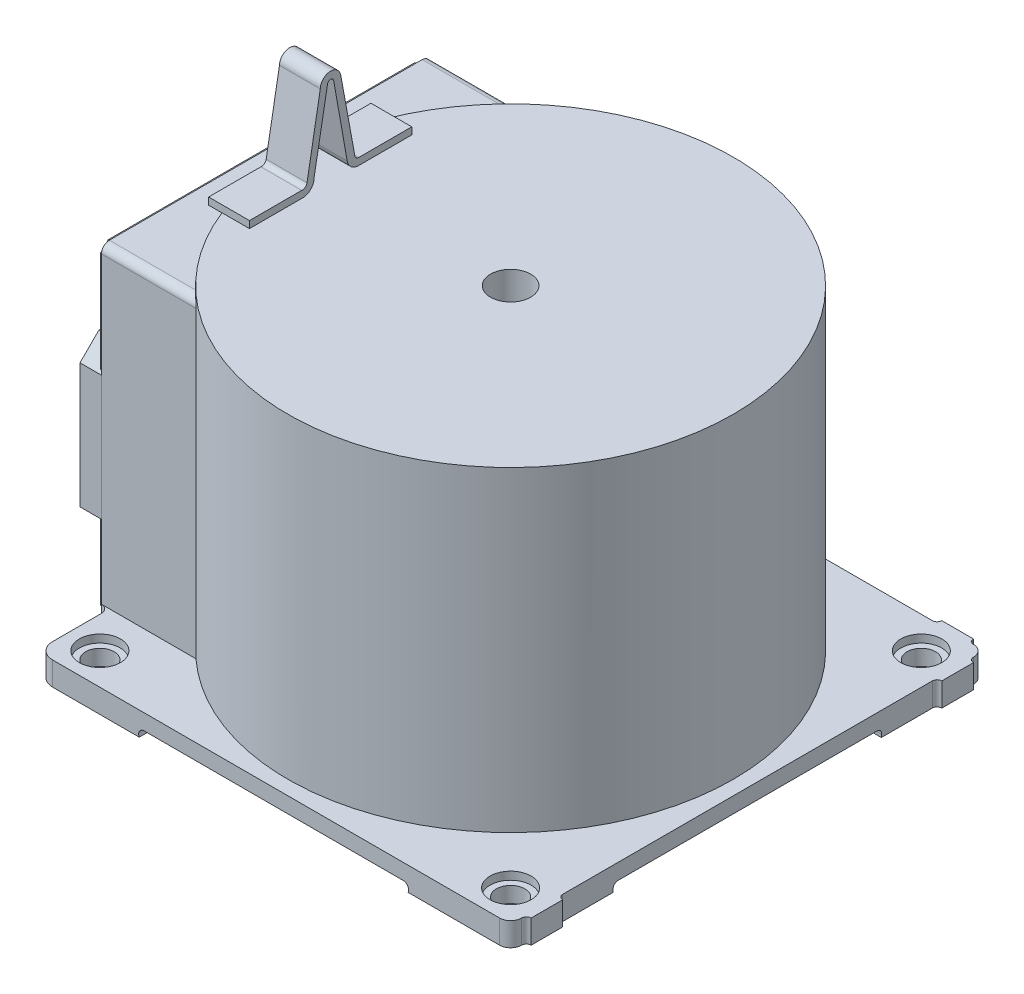
SolidWorks part; units mm, degrees
ref_plane "FRONT" through (0, 0, 0) normal (0, 0, 1) x (1, 0, 0)
ref_plane "TOP" through (0, 0, 0) normal (0, 1, 0) x (1, 0, 0)
ref_plane "SIDE" through (0, 0, 0) normal (1, 0, 0) x (0, 0, -1)
sketch "Sketch1"
sketch "Sketch2"
sketch "Sketch5"
sketch "Sketch3" plane through (0, 0, 0) normal (0, 1, 0) x (1, 0, 0)
  line L0 (140, 153) -> (120, 153)
  line L1 (-117, 150) -> (117, 150)
  line L2 (117, 150) -> (-117, 150) construction
  line L3 (153, 140) -> (153, 120)
  line L4 (150, 117) -> (150, -117)
  line L5 (150, 117) -> (150, -117) construction
  line L6 (153, -120) -> (153, -140)
  line L7 (143, -150) -> (-140, -150)
  line L8 (-140, -150) -> (143, -150) construction
  line L9 (-150, -140) -> (-150, -109)
  line L10 (-155, -104) -> (-155, 104)
  line L11 (-155, 104) -> (-155, -104) construction
  line L12 (-120, 153) -> (-140, 153)
  line L13 (-150, 143) -> (-150, 109)
  arc A0 (117, 150) -> (120, 153) centre (117, 153) ccw
  arc A1 (153, 140) -> (150, 143) centre (153, 143) cw
  arc A2 (150, 143) -> (143, 150) centre (143, 143) ccw
  arc A3 (143, 150) -> (140, 153) centre (143, 153) cw
  arc A4 (150, 117) -> (153, 120) centre (153, 117) cw
  arc A5 (150, -117) -> (153, -120) centre (153, -117) ccw
  arc A6 (153, -140) -> (150, -143) centre (153, -143) ccw
  arc A7 (150, -143) -> (143, -150) centre (143, -143) cw
  arc A8 (-140, -150) -> (-150, -140) centre (-140, -140) cw
  arc A9 (-150, -109) -> (-155, -104) centre (-155, -109) ccw
  arc A10 (-150, 109) -> (-155, 104) centre (-155, 109) cw
  arc A11 (-150, 143) -> (-143, 150) centre (-143, 143) cw
  arc A12 (-143, 150) -> (-140, 153) centre (-143, 153) ccw
  arc A13 (-117, 150) -> (-120, 153) centre (-117, 153) cw
extrude "Base-Extrude" add sketch "Sketch3" along normal blind 14.9225
sketch "Sketch4" plane through (0, 0, 150) normal (0, 0, 1) x (1, 0, 0)
  line L0 (82, 5) -> (-82, 5)
  line L1 (85.09, 0) -> (85.09, -16.51)
  line L2 (85.09, -16.51) -> (-85.09, -16.51)
  line L3 (-85.09, -16.51) -> (-85.09, 0)
  arc A0 (-82, 5) -> (-85.09, 0) centre (-82, 1.5452) ccw
  arc A1 (82, 5) -> (85.09, 0) centre (82, 1.5452) cw
extrude "Cut-Extrude1" cut sketch "Sketch4" against normal through all
sketch "Sketch6" plane through (150, 0, 0) normal (1, 0, 0) x (0, 0, -1)
  line L0 (82.0005, 5.0001) -> (-82.0005, 5.0001)
  line L1 (84.6883, 1.8556) -> (84.6883, -4.2544)
  line L2 (84.6883, -4.2544) -> (-85.09, -4.2544)
  line L3 (-85.09, -4.2544) -> (-85.09, 1.27)
  arc A0 (-82.0005, 5.0001) -> (-85.09, 1.27) centre (-82.0005, 1.8556) ccw
  arc A1 (82.0005, 5.0001) -> (84.6883, 1.8556) centre (82.0005, 2.2792) cw
extrude "Cut-Extrude2" cut sketch "Sketch6" against normal through all
sketch "Sketch7" plane through (0, 14.9225, 0) normal (0, 1, 0) x (-1, 0, 0)
  circle A0 centre (-130, 130) radius 13
  circle A1 centre (-130, -130) radius 13
  circle A2 centre (130, -130) radius 13
  circle A3 centre (130, 130) radius 13
  circle A4 centre (-130, -130) radius 13 construction
  circle A5 centre (-130, 130) radius 13 construction
  circle A6 centre (130, 130) radius 13 construction
  circle A7 centre (130, -130) radius 13 construction
extrude "Cut-Extrude3" cut sketch "Sketch7" against normal blind 5
sketch "Sketch8" plane through (0, 9.9225, 0) normal (0, 1, 0) x (-1, 0, 0)
  circle A0 centre (-130, -130) radius 9
  circle A1 centre (130, -130) radius 9
  circle A2 centre (130, 130) radius 9
  circle A3 centre (-130, 130) radius 9
  circle A4 centre (130, -130) radius 9 construction
  circle A5 centre (-130, -130) radius 9 construction
  circle A6 centre (-130, 130) radius 9 construction
  circle A7 centre (130, 130) radius 9 construction
extrude "Cut-Extrude4" cut sketch "Sketch8" against normal through all
sketch "Sketch9" plane through (0, 14.9225, 0) normal (0, 1, 0) x (-1, 0, 0)
  circle A0 centre (0, 0) radius 141
  circle A1 centre (0, 0) radius 141 construction
extrude "Boss-Extrude1" add sketch "Sketch9" along normal blind 200.152
sketch "Sketch10" plane through (-155, 0, 0) normal (-1, 0, 0) x (0, 0, 1)
  line L0 (99, 212) -> (-99, 212)
  line L1 (-104, 207) -> (-104, 10)
  line L2 (-99, 5) -> (99, 5)
  line L3 (104, 10) -> (104, 207)
  arc A0 (104, 207) -> (99, 212) centre (99, 207) ccw
  arc A1 (-99, 212) -> (-104, 207) centre (-99, 207) ccw
  arc A2 (-104, 10) -> (-99, 5) centre (-99, 10) ccw
  arc A3 (99, 5) -> (104, 10) centre (99, 10) ccw
extrude "Boss-Extrude2" add sketch "Sketch10" against normal up to surface (59.7897 mm away)
sketch "Sketch11" plane through (-155, 0, 0) normal (-1, 0, 0) x (0, 0, 1)
  line L0 (91.5, 152) -> (12.5, 152)
  line L1 (91.5, 152) -> (103.5, 140)
  line L2 (103.5, 140) -> (103.5, 61)
  line L3 (103.5, 61) -> (91.5, 49)
  line L4 (91.5, 49) -> (12.5, 49)
  line L5 (52, 152) -> (52, 112.256) construction
  line L6 (0.5, 140) -> (0.5, 61)
  line L7 (0.5, 140) -> (12.5, 152)
  line L8 (12.5, 49) -> (0.5, 61)
extrude "Boss-Extrude3" add sketch "Sketch11" along normal blind 14.097
sketch "Sketch12" plane through (-155, 0, 0) normal (-1, 0, 0) x (0, 0, 1)
  line L0 (-97, 210) -> (97, 210)
  line L1 (97, 210) -> (102, 205)
  line L2 (102, 205) -> (102, 12)
  line L3 (102, 12) -> (97, 7)
  line L4 (97, 7) -> (-77, 7)
  line L5 (-77, 7) -> (-82, 12)
  line L6 (-82, 12) -> (-82, 26)
  line L7 (-82, 26) -> (-97, 26)
  line L8 (-97, 26) -> (-102, 31)
  line L9 (-102, 31) -> (-102, 205)
  line L10 (-102, 205) -> (-97, 210)
extrude "Boss-Extrude4" add sketch "Sketch12" along normal blind 2.667
sketch "Sketch13" plane through (-157.667, 0, 0) normal (-1, 0, 0) x (0, 0, 1)
  line L0 (-11.5, 119) -> (-11.5, 152)
  line L1 (-16.5, 157) -> (-79.5, 157)
  line L2 (-84.5, 152) -> (-84.5, 119)
  line L4 (-79.5, 114) -> (-16.5, 114)
  line L5 (-79.5, 87.5) -> (-16.5, 87.5)
  line L6 (-11.5, 82.5) -> (-11.5, 49.5)
  line L8 (-16.5, 44.5) -> (-79.5, 44.5)
  line L9 (-84.5, 49.5) -> (-84.5, 82.5)
  arc A0 (-16.5, 157) -> (-11.5, 152) centre (-16.5, 152) cw
  arc A1 (-11.5, 119) -> (-16.5, 114) centre (-16.5, 119) cw
  arc A2 (-79.5, 114) -> (-84.5, 119) centre (-79.5, 119) cw
  arc A3 (-84.5, 152) -> (-79.5, 157) centre (-79.5, 152) cw
  arc A4 (-84.5, 82.5) -> (-79.5, 87.5) centre (-79.5, 82.5) cw
  arc A5 (-16.5, 87.5) -> (-11.5, 82.5) centre (-16.5, 82.5) cw
  arc A6 (-11.5, 49.5) -> (-16.5, 44.5) centre (-16.5, 49.5) cw
  arc A7 (-79.5, 44.5) -> (-84.5, 49.5) centre (-79.5, 49.5) cw
extrude "Boss-Extrude5" add sketch "Sketch13" along normal blind 34.0995
sketch "Sketch14" plane through (-191.7665, 0, 0) normal (-1, 0, 0) x (0, 0, 1)
  line L0 (-80.5, 152) -> (-80.5, 119) construction
  line L1 (-80.5, 153) -> (-15.5, 153)
  line L2 (-80.5, 153) -> (-80.5, 118)
  line L3 (-80.5, 118) -> (-15.5, 118)
  line L4 (-15.5, 153) -> (-15.5, 118)
  line L5 (-80.5, 48.5) -> (-15.5, 48.5)
  line L6 (-80.5, 48.5) -> (-80.5, 83.5)
  line L7 (-80.5, 83.5) -> (-15.5, 83.5)
  line L8 (-15.5, 48.5) -> (-15.5, 83.5)
  line L9 (-15.5, 119) -> (-15.5, 152) construction
  line L10 (-79.5, 153) -> (-48, 153) construction
  line L11 (-79.5, 118) -> (-48, 118) construction
  line L12 (-79.5, 83.5) -> (-48, 83.5) construction
  line L13 (-79.5, 48.5) -> (-48, 48.5) construction
  line L14 (-61.5, 124.25) -> (-57.0042, 124.25) construction
  line L15 (-61.5, 124.25) -> (-61.5, 128.7458) construction
  line L16 (-61.5, 54.75) -> (-57.0042, 54.75) construction
  line L17 (-61.5, 54.75) -> (-61.5, 59.2458) construction
  circle A0 centre (-61.5, 124.25) radius 1.75
  circle A1 centre (-61.5, 124.25) radius 1.75 construction
  circle A2 centre (-57.0042, 124.25) radius 1.75
  circle A3 centre (-52.5084, 124.25) radius 1.75
  circle A4 centre (-48.0126, 124.25) radius 1.75
  circle A5 centre (-43.5168, 124.25) radius 1.75
  circle A6 centre (-39.021, 124.25) radius 1.75
  circle A7 centre (-34.5252, 124.25) radius 1.75
  circle A8 centre (-61.5, 128.7458) radius 1.75
  circle A9 centre (-57.0042, 128.7458) radius 1.75
  circle A10 centre (-52.5084, 128.7458) radius 1.75
  circle A11 centre (-48.0126, 128.7458) radius 1.75
  circle A12 centre (-43.5168, 128.7458) radius 1.75
  circle A13 centre (-39.021, 128.7458) radius 1.75
  circle A14 centre (-34.5252, 128.7458) radius 1.75
  circle A15 centre (-61.5, 133.2416) radius 1.75
  circle A16 centre (-57.0042, 133.2416) radius 1.75
  circle A17 centre (-52.5084, 133.2416) radius 1.75
  circle A18 centre (-48.0126, 133.2416) radius 1.75
  circle A19 centre (-43.5168, 133.2416) radius 1.75
  circle A20 centre (-39.021, 133.2416) radius 1.75
  circle A21 centre (-34.5252, 133.2416) radius 1.75
  circle A22 centre (-61.5, 137.7374) radius 1.75
  circle A23 centre (-57.0042, 137.7374) radius 1.75
  circle A24 centre (-52.5084, 137.7374) radius 1.75
  circle A25 centre (-48.0126, 137.7374) radius 1.75
  circle A26 centre (-43.5168, 137.7374) radius 1.75
  circle A27 centre (-39.021, 137.7374) radius 1.75
  circle A28 centre (-34.5252, 137.7374) radius 1.75
  circle A29 centre (-61.5, 142.2332) radius 1.75
  circle A30 centre (-57.0042, 142.2332) radius 1.75
  circle A31 centre (-52.5084, 142.2332) radius 1.75
  circle A32 centre (-48.0126, 142.2332) radius 1.75
  circle A33 centre (-43.5168, 142.2332) radius 1.75
  circle A34 centre (-39.021, 142.2332) radius 1.75
  circle A35 centre (-34.5252, 142.2332) radius 1.75
  circle A36 centre (-61.5, 146.729) radius 1.75
  circle A37 centre (-57.0042, 146.729) radius 1.75
  circle A38 centre (-52.5084, 146.729) radius 1.75
  circle A39 centre (-48.0126, 146.729) radius 1.75
  circle A40 centre (-43.5168, 146.729) radius 1.75
  circle A41 centre (-39.021, 146.729) radius 1.75
  circle A42 centre (-34.5252, 146.729) radius 1.75
  circle A43 centre (-61.5, 54.75) radius 1.75
  circle A44 centre (-61.5, 54.75) radius 1.75 construction
  circle A45 centre (-57.0042, 54.75) radius 1.75
  circle A46 centre (-52.5084, 54.75) radius 1.75
  circle A47 centre (-48.0126, 54.75) radius 1.75
  circle A48 centre (-43.5168, 54.75) radius 1.75
  circle A49 centre (-39.021, 54.75) radius 1.75
  circle A50 centre (-34.5252, 54.75) radius 1.75
  circle A51 centre (-61.5, 59.2458) radius 1.75
  circle A52 centre (-57.0042, 59.2458) radius 1.75
  circle A53 centre (-52.5084, 59.2458) radius 1.75
  circle A54 centre (-48.0126, 59.2458) radius 1.75
  circle A55 centre (-43.5168, 59.2458) radius 1.75
  circle A56 centre (-39.021, 59.2458) radius 1.75
  circle A57 centre (-34.5252, 59.2458) radius 1.75
  circle A58 centre (-61.5, 63.7416) radius 1.75
  circle A59 centre (-57.0042, 63.7416) radius 1.75
  circle A60 centre (-52.5084, 63.7416) radius 1.75
  circle A61 centre (-48.0126, 63.7416) radius 1.75
  circle A62 centre (-43.5168, 63.7416) radius 1.75
  circle A63 centre (-39.021, 63.7416) radius 1.75
  circle A64 centre (-34.5252, 63.7416) radius 1.75
  circle A65 centre (-61.5, 68.2374) radius 1.75
  circle A66 centre (-57.0042, 68.2374) radius 1.75
  circle A67 centre (-52.5084, 68.2374) radius 1.75
  circle A68 centre (-48.0126, 68.2374) radius 1.75
  circle A69 centre (-43.5168, 68.2374) radius 1.75
  circle A70 centre (-39.021, 68.2374) radius 1.75
  circle A71 centre (-34.5252, 68.2374) radius 1.75
  circle A72 centre (-61.5, 72.7332) radius 1.75
  circle A73 centre (-57.0042, 72.7332) radius 1.75
  circle A74 centre (-52.5084, 72.7332) radius 1.75
  circle A75 centre (-48.0126, 72.7332) radius 1.75
  circle A76 centre (-43.5168, 72.7332) radius 1.75
  circle A77 centre (-39.021, 72.7332) radius 1.75
  circle A78 centre (-34.5252, 72.7332) radius 1.75
  circle A79 centre (-61.5, 77.229) radius 1.75
  circle A80 centre (-57.0042, 77.229) radius 1.75
  circle A81 centre (-52.5084, 77.229) radius 1.75
  circle A82 centre (-48.0126, 77.229) radius 1.75
  circle A83 centre (-43.5168, 77.229) radius 1.75
  circle A84 centre (-39.021, 77.229) radius 1.75
  circle A85 centre (-34.5252, 77.229) radius 1.75
  dimension "D1" = 90
  dimension "D2" = 90
extrude "Cut-Extrude5" cut sketch "Sketch14" against normal blind 17.272
ref_plane "Plane1" through (-139.7855, 0, 0) normal (1, 0, 0) x (0, 0, -1)
sketch "Sketch15" plane through (-139.7855, 0, 0) normal (1, 0, 0) x (0, 0, -1)
  line L0 (51.3877, 215) -> (51.3877, 219.5)
  line L1 (51.3877, 219.5) -> (17.8926, 219.5)
  line L2 (15.24, 222.25) -> (6.4013, 270.3944)
  line L3 (-6.5428, 269.216) -> (-14.9382, 221.9791)
  line L4 (-18.3045, 219.5) -> (-51.3877, 219.5)
  line L5 (-51.3877, 219.5) -> (-51.3877, 215)
  line L6 (-51.3877, 215) -> (-36.9172, 215)
  line L7 (141, 215) -> (-141, 215) construction
  line L8 (-36.9172, 215) -> (-36.9172, 213.336)
  line L9 (-36.9172, 213.336) -> (-31.5223, 213.336)
  line L10 (-31.5223, 213.336) -> (-31.5223, 215)
  line L11 (-31.5223, 215) -> (-17.8926, 215)
  line L12 (-10.4685, 222.4241) -> (-1.9696, 269.613)
  line L13 (1.9276, 269.6075) -> (10.5065, 221.1976)
  line L14 (17.8991, 215) -> (51.3877, 215)
  arc A0 (17.8926, 219.5) -> (15.24, 222.25) centre (17.8926, 222.1543) cw
  arc A1 (6.4013, 270.3944) -> (-6.5428, 269.216) centre (-0.0172, 269.216) ccw
  arc A2 (-14.9382, 221.9791) -> (-18.3045, 219.5) centre (-17.9251, 222.5099) cw
  arc A3 (-17.8926, 215) -> (-10.4685, 222.4241) centre (-17.8926, 222.4241) ccw
  arc A4 (-1.9696, 269.613) -> (1.9276, 269.6075) centre (-0.0215, 269.2621) cw
  arc A5 (10.5065, 221.1976) -> (17.8991, 215) centre (17.8991, 222.5077) ccw
extrude "Boss-Extrude6" add sketch "Sketch15" along normal blind 25.8445
sketch "Sketch16" plane through (0, 215.0745, 0) normal (0, 1, 0) x (-1, 0, 0)
  circle A0 centre (0, 0) radius 12.7
extrude "Cut-Extrude6" cut sketch "Sketch16" against normal through all
